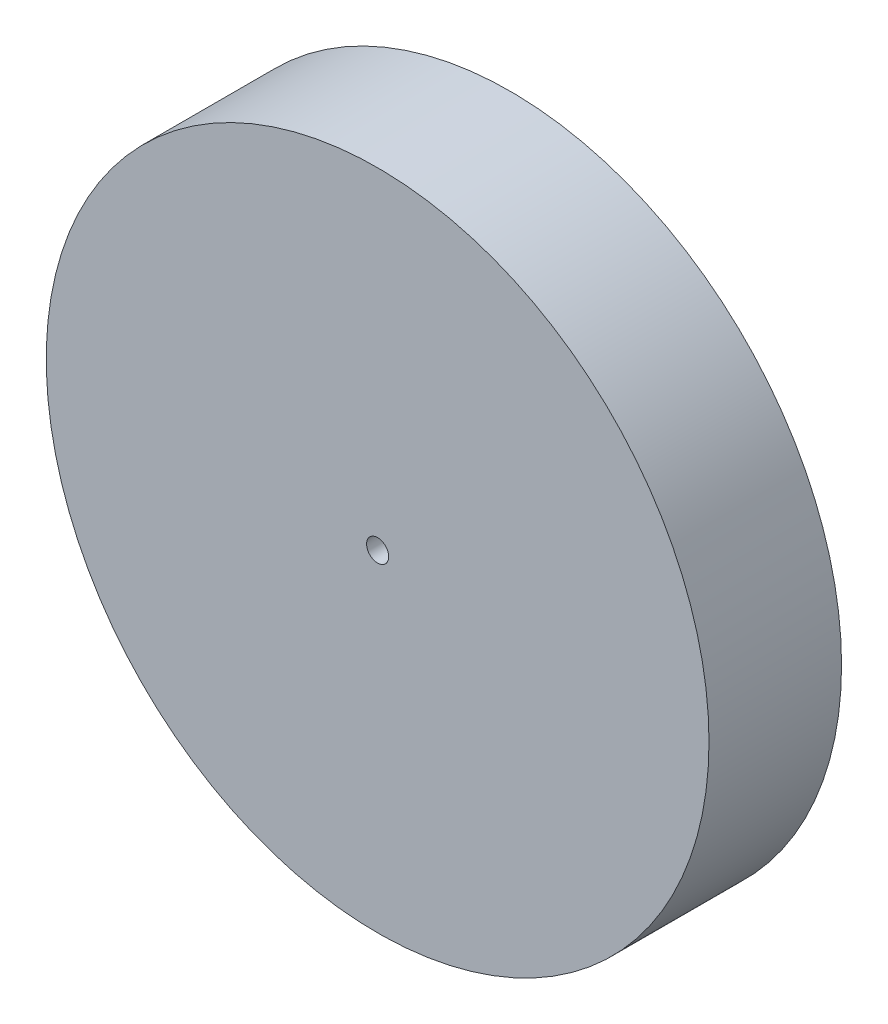
SolidWorks part; units mm, degrees
ref_plane "Front Plane" through (0, 0, 0) normal (0, 0, 1) x (1, 0, 0)
ref_plane "Top Plane" through (0, 0, 0) normal (0, 1, 0) x (1, 0, 0)
ref_plane "Right Plane" through (0, 0, 0) normal (1, 0, 0) x (0, 0, -1)
sketch "Sketch1" plane through (0, 0, 0) normal (0, 0, 1) x (1, 0, 0)
  circle A0 centre (0, 0) radius 75
  dimension "D1" = 150
extrude "Boss-Extrude1" add sketch "Sketch1" along normal blind 30
sketch "Sketch2" plane through (0, 0, 0) normal (0, 0, -1) x (-1, 0, 0)
  circle A0 centre (0, 0) radius 2.5
  dimension "D1" = 5
extrude "Cut-Extrude1" cut sketch "Sketch2" against normal through all
shell "Shell1" thickness 10
